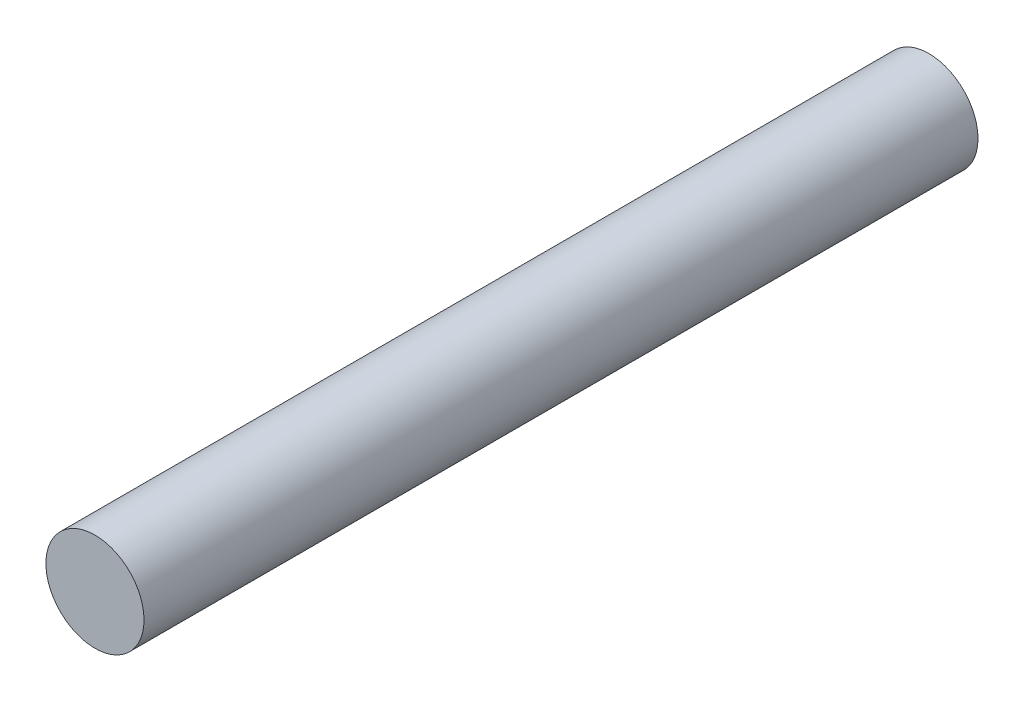
SolidWorks part; units mm, degrees
ref_plane "Front Plane" through (0, 0, 0) normal (0, 0, 1) x (1, 0, 0)
ref_plane "Top Plane" through (0, 0, 0) normal (0, 1, 0) x (1, 0, 0)
ref_plane "Right Plane" through (0, 0, 0) normal (1, 0, 0) x (0, 0, -1)
sketch "Sketch1" plane through (0, 0, 0) normal (0, 0, 1) x (1, 0, 0)
  circle A0 centre (0, 0) radius 5
extrude "Boss-Extrude1" add sketch "Sketch1" along normal blind 85
